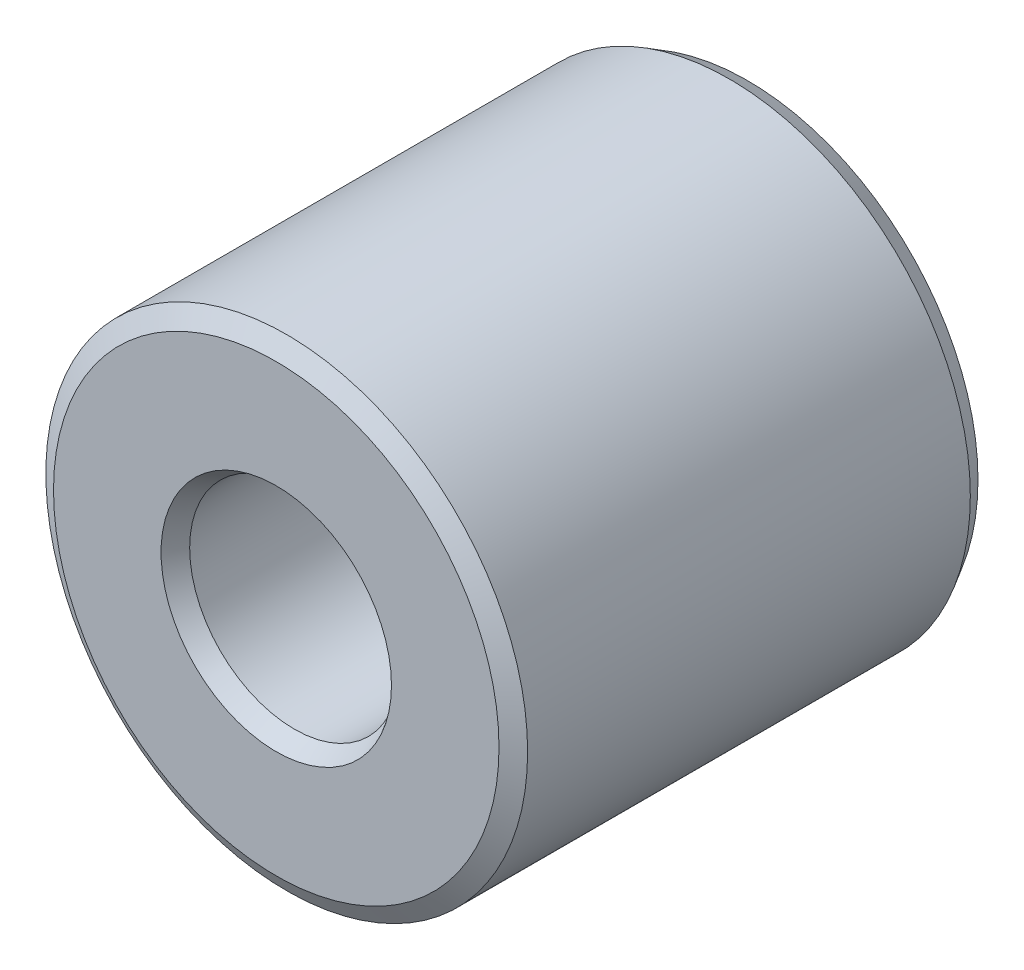
SolidWorks part; units mm, degrees
material "PA Typ 6"
ref_plane "Płaszczyzna przednia" through (0, 0, 0) normal (0, 0, 1) x (1, 0, 0)
ref_plane "Płaszczyzna górna" through (0, 0, 0) normal (0, 1, 0) x (1, 0, 0)
ref_plane "Płaszczyzna prawa" through (0, 0, 0) normal (1, 0, 0) x (0, 0, -1)
sketch "Szkic1" plane through (0, 0, 0) normal (0, 0, 1) x (1, 0, 0)
  circle A0 centre (0, 0) radius 2.3
  circle A1 centre (0, 0) radius 1
  dimension "D1" = 2
  dimension "D2" = 4.6
extrude "Dodanie-wyciągnięcie1" add sketch "Szkic1" along normal blind 4.5
chamfer "Sfazowanie1" distance 0.1 angle 60 4 edges at (2.3, 0, 0) (2.3, 0, 4.5) (1, 0, 0) (1, 0, 4.5)
ref_plane "Płaszczyzna1" through (0, 0, 2.25) normal (0, 0, 1) x (1, 0, 0)
